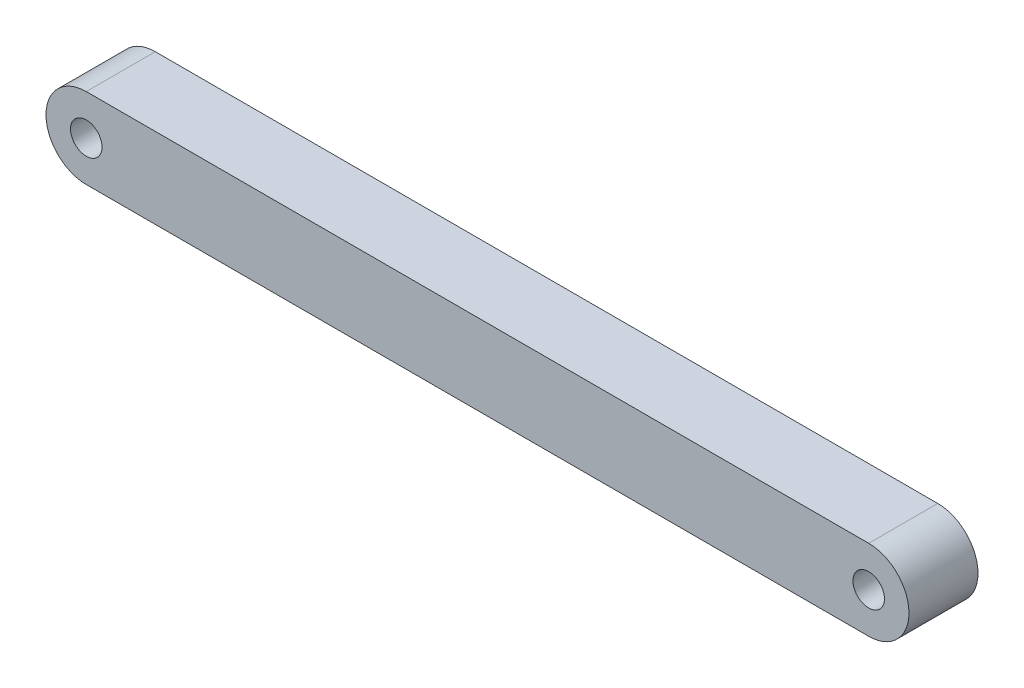
SolidWorks part; units mm, degrees
ref_plane "Front Plane" through (0, 0, 0) normal (0, 0, 1) x (1, 0, 0)
ref_plane "Top Plane" through (0, 0, 0) normal (0, 1, 0) x (1, 0, 0)
ref_plane "Right Plane" through (0, 0, 0) normal (1, 0, 0) x (0, 0, -1)
sketch "Sketch1" plane through (0, 0, 0) normal (0, 0, 1) x (1, 0, 0)
  line L0 (0, 0) -> (86.36, 0) construction
  line L1 (0, 4.445) -> (86.36, 4.445)
  line L2 (0, -4.445) -> (86.36, -4.445)
  arc A0 (0, 4.445) -> (0, -4.445) centre (0, 0) ccw
  arc A1 (86.36, -4.445) -> (86.36, 4.445) centre (86.36, 0) ccw
  point P3 (43.18, 0)
  dimension "D1" = 4.445
  dimension "D2" = 86.36
extrude "Boss-Extrude1" add sketch "Sketch1" along normal blind 7.62
sketch "Sketch2" plane through (0, 0, 7.62) normal (0, 0, 1) x (1, 0, 0)
  circle A0 centre (0, 0) radius 1.7399
  dimension "D1" = 3.4798
extrude "Cut-Extrude1" cut sketch "Sketch2" against normal through all both and the other way through all
ref_plane "Plane1" through (43.18, 0, 0) normal (1, 0, 0) x (0, 0, -1)
mirror "Mirror1" about plane through (43.18, 0, 0) normal (1, 0, 0) of "Cut-Extrude1"
